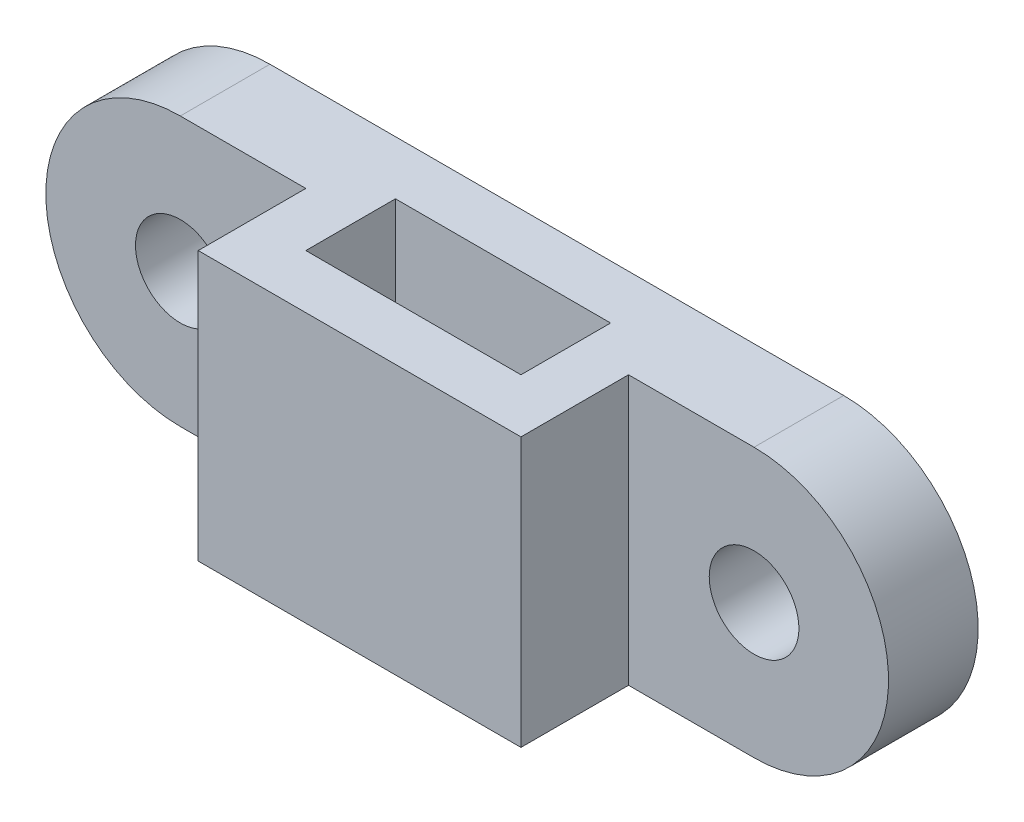
SolidWorks part; units mm, degrees
ref_plane "Front Plane" through (0, 0, 0) normal (0, 0, 1) x (1, 0, 0)
ref_plane "Top Plane" through (0, 0, 0) normal (0, 1, 0) x (1, 0, 0)
ref_plane "Right Plane" through (0, 0, 0) normal (1, 0, 0) x (0, 0, -1)
sketch "Sketch1" plane through (0, 0, 0) normal (0, 1, 0) x (1, 0, 0)
  line L1 (0, 0) -> (12, 0)
  line L2 (0, 0) -> (0, -5)
  line L3 (0, -5) -> (12, -5)
  line L4 (12, 0) -> (12, -5)
  line L5 (-3, 3) -> (15, 3)
  line L6 (-3, 3) -> (-3, -8)
  line L7 (-3, -8) -> (15, -8)
  line L8 (15, 3) -> (15, -8)
  dimension "D1" = 12
  dimension "D2" = 5
  dimension "D3" = 3
  dimension "D4" = 3
  dimension "D5" = 3
  dimension "D6" = 3
extrude "Boss-Extrude1" add sketch "Sketch1" along normal blind 15
sketch "Sketch2" plane through (0, 0, -3) normal (0, 0, -1) x (-1, 0, 0)
  line L0 (3, 15) -> (3, 0) construction
  line L1 (-15, 15) -> (-15, 0) construction
  line L2 (3, 15) -> (3, 0)
  line L3 (-15, 15) -> (-15, 0)
  line L4 (-15, 15) -> (-22, 15)
  line L5 (-15, 0) -> (-22, 0)
  line L6 (3, 15) -> (10, 15)
  line L7 (3, 0) -> (10, 0)
  arc A0 (-22, 15) -> (-22, 0) centre (-22, 7.5) ccw
  arc A1 (10, 15) -> (10, 0) centre (10, 7.5) cw
  circle A2 centre (-22, 7.5) radius 2.5
  circle A3 centre (10, 7.5) radius 2.5
  line M11 (3, 0) -> (3, 15)
  line M13 (-15, 15) -> (-15, 0)
  dimension "D2" = 5
  dimension "D3" = 5
  dimension "D1" = 7
extrude "Boss-Extrude2" add sketch "Sketch2" against normal blind 5 contours A1 L6 L7 A3 M11 | L4 A0 L5 A2 M13
ref_plane "Plane1" through (0, 5, 0) normal (0, -1, 0) x (-1, 0, 0)
sketch "Sketch3" plane through (0, 5, 0) normal (0, -1, 0) x (-1, 0, 0)
  line L0 (-12, -5) -> (-12, 0) construction
  line L1 (-12, 0) -> (0, 0) construction
  line L2 (0, 0) -> (0, -5) construction
  line L3 (0, -5) -> (-12, -5) construction
  line L4 (-12, -2.8284) -> (-12, 0)
  line L5 (-12, 0) -> (-9.1716, 0)
  line L6 (0, -2.1716) -> (0, -5)
  line L7 (0, -5) -> (-2.8284, -5)
  line L8 (0, -2.1716) -> (-2.8284, -5)
  line L9 (-9.1716, 0) -> (-12, -2.8284)
  dimension "D1" = 2
extrude "Boss-Extrude3" add sketch "Sketch3" against normal blind 2
